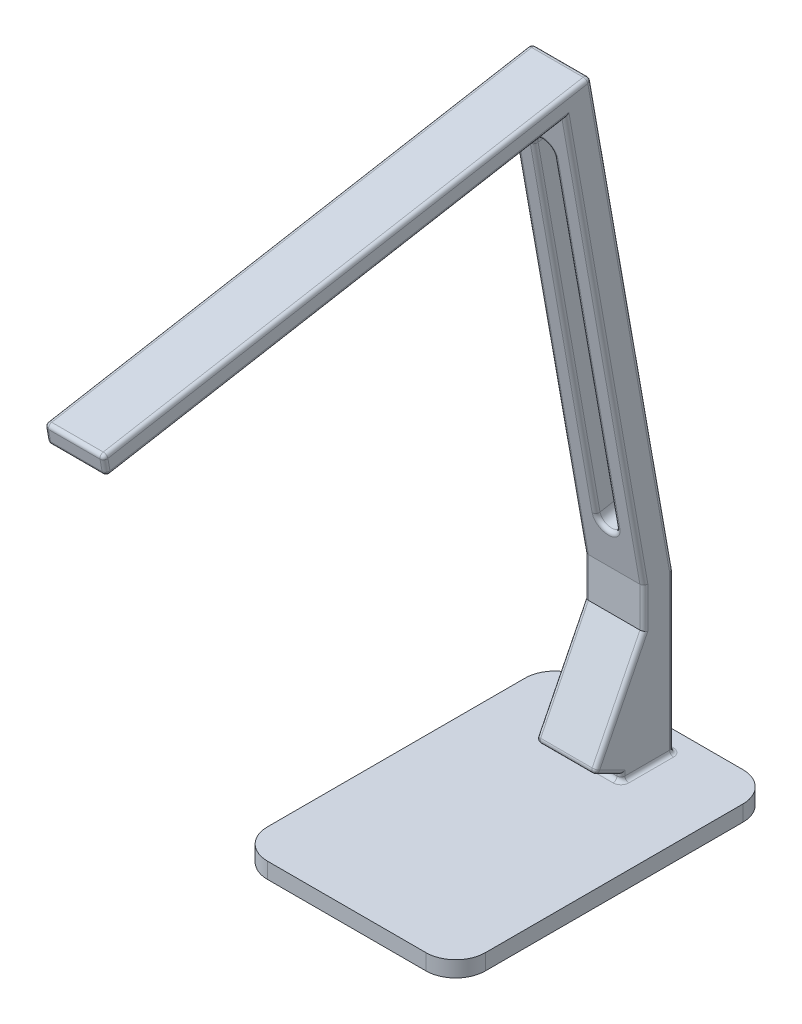
SolidWorks part; units mm, degrees
ref_plane "Front Plane" through (0, 0, 0) normal (0, 0, 1) x (1, 0, 0)
ref_plane "Top Plane" through (0, 0, 0) normal (0, 1, 0) x (1, 0, 0)
ref_plane "Right Plane" through (0, 0, 0) normal (1, 0, 0) x (0, 0, -1)
sketch "Sketch1" plane through (0, 0, 0) normal (0, 1, 0) x (1, 0, 0)
  line L1 (-69.85, -101.6) -> (69.85, -101.6)
  line L2 (-69.85, -101.6) -> (-69.85, 101.6)
  line L3 (-69.85, 101.6) -> (69.85, 101.6)
  line L4 (69.85, -101.6) -> (69.85, 101.6)
  line L5 (-69.85, -101.6) -> (69.85, 101.6) construction
  line L6 (-69.85, 101.6) -> (69.85, -101.6) construction
  point P0 (0, 0)
  dimension "D1" = 203.2
  dimension "D2" = 139.7
extrude "Boss-Extrude1" add sketch "Sketch1" along normal blind 10.16
sketch "Sketch2" plane through (0, 10.16, 0) normal (0, 1, 0) x (1, 0, 0)
  line L1 (-19.05, 88.9) -> (19.05, 88.9)
  line L2 (-19.05, 88.9) -> (-19.05, 38.1)
  line L3 (-19.05, 38.1) -> (19.05, 38.1)
  line L4 (19.05, 88.9) -> (19.05, 38.1)
  line L5 (-19.05, 88.9) -> (19.05, 38.1) construction
  line L6 (-19.05, 38.1) -> (19.05, 88.9) construction
  line L7 (69.85, 101.6) -> (-69.85, 101.6) construction
  point P0 (0, 63.5)
  point P5 (0, 0)
  point P7 (0, 0)
  dimension "D1" = 38.1
  dimension "D2" = 38.1
  dimension "D3" = 50.8
extrude "Boss-Extrude2" add sketch "Sketch2" along normal blind 76.2
sketch "Sketch3" plane through (-19.05, 0, 0) normal (-1, 0, 0) x (0, 0, 1)
  line L0 (-69.85, 86.36) -> (-38.1, 22.86)
  line L1 (-88.9, 86.36) -> (-38.1, 86.36) construction
  line L2 (-38.1, 86.36) -> (-38.1, 10.16) construction
  line L3 (-69.85, 86.36) -> (-38.1, 86.36)
  line L4 (-38.1, 86.36) -> (-38.1, 22.86)
  line L6 (-101.6, 10.16) -> (101.6, 10.16) construction
  line L7 (-38.1, 22.86) -> (-55.1388, 14.3406)
  line L8 (-55.1388, 14.3406) -> (-55.1388, 10.16)
  line L9 (-88.9, 10.16) -> (-38.1, 10.16) construction
  line L10 (-55.1388, 10.16) -> (-38.1, 10.16)
  line L11 (-38.1, 10.16) -> (-38.1, 22.86)
  line L12 (-38.1, 10.16) -> (-38.1, 22.86)
  line M2 (-88.9, 10.16) -> (-38.1, 10.16)
  line M3 (-38.1, 10.16) -> (-38.1, 86.36)
  line M4 (-38.1, 86.36) -> (-88.9, 86.36)
  dimension "D1" = 19.05
  dimension "D2" = 12.7
  dimension "D3" = 19.05
extrude "Cut-Extrude1" cut sketch "Sketch3" against normal through all contours L7 L8 M2 M3 | L0 M4 M3
sketch "Sketch4" plane through (0, 86.36, 0) normal (0, 1, 0) x (1, 0, 0)
  line L4 (-19.05, 69.85) -> (19.05, 69.85)
  line L5 (19.05, 69.85) -> (19.05, 88.9)
  line L6 (19.05, 88.9) -> (-19.05, 88.9)
  line L7 (-19.05, 88.9) -> (-19.05, 69.85)
  line L8 (-19.05, 69.85) -> (19.05, 69.85)
  line L9 (19.05, 69.85) -> (19.05, 88.9)
  line L10 (19.05, 88.9) -> (-19.05, 88.9)
  line L11 (-19.05, 88.9) -> (-19.05, 69.85)
  dimension "D1" = 0
extrude "Boss-Extrude3" add sketch "Sketch4" along normal blind 25.4
sketch "Sketch5" plane through (-19.05, 0, 0) normal (-1, 0, 0) x (0, 0, 1)
  line L0 (-88.9, 111.76) -> (-38.1774, 399.4223)
  line L1 (-38.1774, 399.4223) -> (-19.7018, 396.1646)
  line L2 (-19.7018, 396.1646) -> (-69.85, 111.76)
  line L3 (-88.9, 111.76) -> (-69.85, 111.76) construction
  line L4 (-88.9, 111.76) -> (-69.85, 111.76)
  dimension "D1" = 292.1
  dimension "D2" = 80
extrude "Boss-Extrude4" add sketch "Sketch5" against normal up to surface (38.1 mm away) up to face at (19.05, 52.4858, -66.554)
sketch "Sketch6" plane through (0, 15.315, -86.8559) normal (0, -0.1736, 0.9848) x (1, 0, 0)
  line L0 (0, 356.6288) -> (0, 128.0288) construction
  line L1 (6.35, 356.6288) -> (6.35, 128.0288)
  line L2 (-6.35, 356.6288) -> (-6.35, 128.0288)
  line L3 (-19.05, 242.3288) -> (118.6634, 242.3288) construction
  line L4 (-19.05, 97.9328) -> (-19.05, 386.7248) construction
  arc A0 (6.35, 356.6288) -> (-6.35, 356.6288) centre (0, 356.6288) ccw
  arc A1 (-6.35, 128.0288) -> (6.35, 128.0288) centre (0, 128.0288) ccw
  point P3 (0, 242.3288)
  point P8 (0, 0)
  dimension "D1" = 12.7
  dimension "D2" = 228.6
extrude "Cut-Extrude2" cut sketch "Sketch6" against normal through all
sketch "Sketch7" plane through (0, 18.5728, -105.3314) normal (0, -0.1736, 0.9848) x (1, 0, 0)
  line L0 (19.05, 386.7248) -> (19.05, 97.9328) construction
  line L1 (-19.05, 386.7248) -> (19.05, 386.7248)
  line L2 (-19.05, 386.7248) -> (-19.05, 399.4248)
  line L3 (-19.05, 399.4248) -> (19.05, 399.4248)
  line L4 (19.05, 386.7248) -> (19.05, 399.4248)
  dimension "D1" = 12.7
extrude "Boss-Extrude5" add sketch "Sketch7" along normal blind 317.5
fillet "Fillet1" radius 2.54 37 edges at (0, 10.16, -55.1388) (-6.35, 253.9623, -44.7759) (0, 372.7794, -23.8252) (6.35, 253.9623, -44.7759) (6.35, 257.22, -63.2515) (0, 376.0371, -42.3008) (-6.35, 257.22, -63.2515) (19.05, 60.96, -88.9) (0, 111.76, -88.9) (-19.05, 60.96, -88.9) (0, 10.16, -88.9) (0, 356.7961, 276.7044) (19.05, 350.5426, 275.6018) (0, 344.289, 274.4991) (-19.05, 350.5426, 275.6018) (0, 135.1452, -65.7266) (0, 138.403, -84.2021) (0, 22.86, -38.1) (0, 411.9294, -35.972) (-19.05, 384.3628, 120.3662) (19.05, 384.3628, 120.3662) (19.05, 370.2268, 127.3986) (-19.05, 370.2268, 127.3986) (19.05, 253.9623, -44.7759) (-19.05, 253.9623, -44.7759) (19.05, 261.8447, -62.436) (-19.05, 261.8447, -62.436) (19.05, 99.06, -69.85) (-19.05, 99.06, -69.85) (-19.05, 54.61, -53.975) (19.05, 54.61, -53.975) (-19.05, 18.6003, -46.6194) (-19.05, 12.2503, -55.1388) (19.05, 18.6003, -46.6194) (19.05, 12.2503, -55.1388) (19.05, 10.16, -72.0194) (-19.05, 10.16, -72.0194)
fillet "Fillet2" radius 19.05 4 edges at (69.85, 5.08, 101.6) (-69.85, 5.08, -101.6) (69.85, 5.08, -101.6) (-69.85, 5.08, 101.6)
